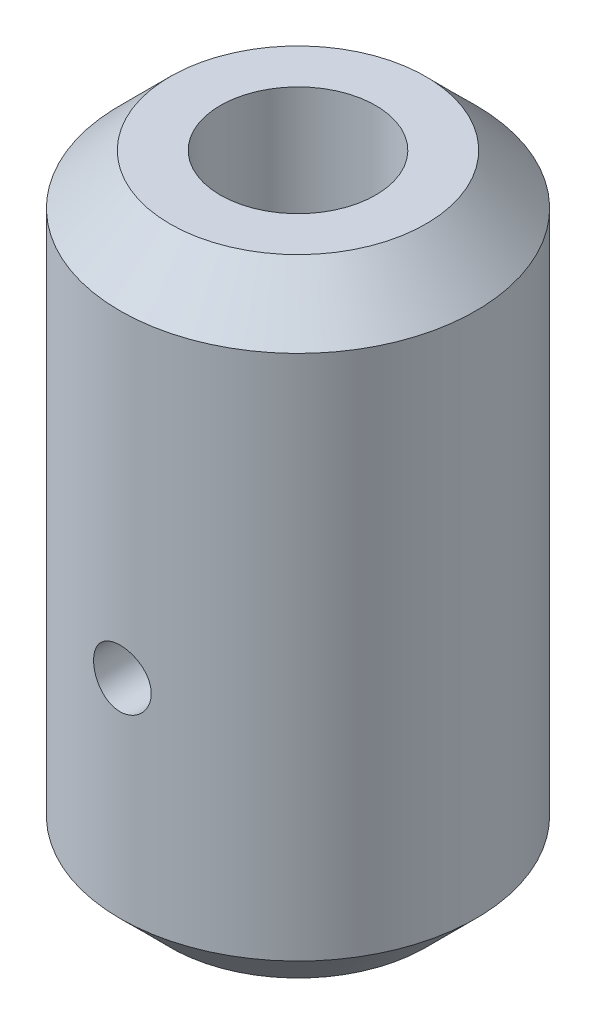
SolidWorks part; units mm, degrees
ref_plane "Front Plane" through (0, 0, 0) normal (0, 0, 1) x (1, 0, 0)
ref_plane "Top Plane" through (0, 0, 0) normal (0, 1, 0) x (1, 0, 0)
ref_plane "Right Plane" through (0, 0, 0) normal (1, 0, 0) x (0, 0, -1)
sketch "Sketch1" plane through (0, 0, 0) normal (0, 1, 0) x (1, 0, 0)
  circle A0 centre (0, 0) radius 3.1
  circle A1 centre (0, 0) radius 7.1
  dimension "D1" = 6.2
  dimension "D2" = 4
extrude "Boss-Extrude1" add sketch "Sketch1" along normal blind 20
sketch "Sketch3" plane through (0, 0, 0) normal (0, 0, 1) x (1, 0, 0)
  line L0 (0, 0) -> (0, 20) construction
  line L1 (-7.1, 0) -> (7.1, 0) construction
  line L2 (7.1, 20) -> (-7.1, 20) construction
  circle A0 centre (0, 5.3) radius 1.15
  dimension "D1" = 2.3
  dimension "D2" = 5.3
extrude "Cut-Extrude1" cut sketch "Sketch3" against normal through all and the other way through all
sketch "Sketch5" plane through (0, 0, 0) normal (0, 0, 1) x (1, 0, 0)
  circle A0 centre (0, 5.3) radius 1.8
  dimension "D1" = 3.6
extrude "Cut-Extrude2" cut sketch "Sketch5" against normal blind 5 from offset 4 offset against normal yes
sketch "Sketch2" plane through (0, 0, 0) normal (0, -1, 0) x (1, 0, 0)
  circle A0 centre (0, 0) radius 7.1
  circle A1 centre (0, 0) radius 7.1 construction
extrude "Boss-Extrude2" add sketch "Sketch2" along normal blind 5
chamfer "Chamfer1" distance 2 angle 45 2 edges at (0, 20, 7.1) (0, -5, -7.1)
